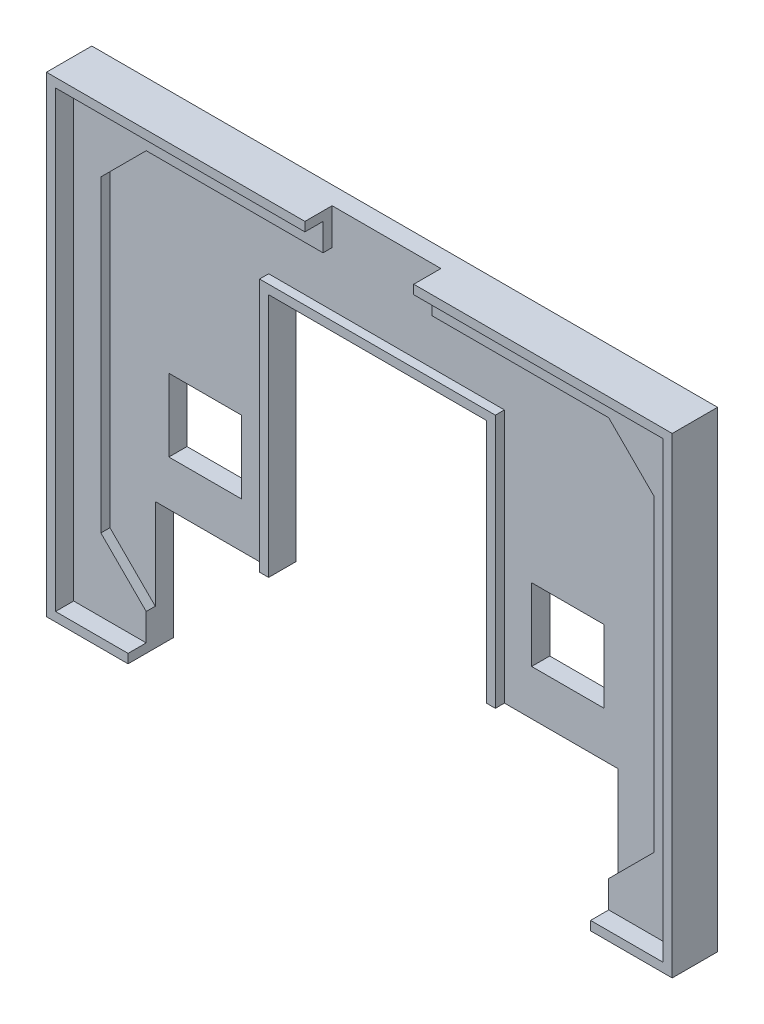
SolidWorks part; units mm, degrees
ref_plane "Přední rovina" through (0, 0, 0) normal (0, 0, 1) x (1, 0, 0)
ref_plane "Horní rovina" through (0, 0, 0) normal (0, 1, 0) x (1, 0, 0)
ref_plane "Pravá rovina" through (0, 0, 0) normal (1, 0, 0) x (0, 0, -1)
sketch "Skica1" plane through (0, 0, 0) normal (0, 0, 1) x (1, 0, 0)
  line L1 (-33.5, -25) -> (33.5, -25)
  line L2 (-33.5, -25) -> (-33.5, 25)
  line L3 (-33.5, 25) -> (33.5, 25)
  line L4 (33.5, -25) -> (33.5, 25)
  line L5 (-33.5, -25) -> (33.5, 25) construction
  line L6 (-33.5, 25) -> (33.5, -25) construction
  point P0 (0, 0)
  dimension "D1" = 67
  dimension "D2" = 50
extrude "Přidat vysunutím1" add sketch "Skica1" along normal blind 3
sketch "Skica2" plane through (0, 0, 3) normal (0, 0, 1) x (1, 0, 0)
  line L0 (-1000, 0) -> (49000, 0) construction
  line L1 (0, -1000) -> (0, 49000) construction
  line L2 (-1000, -22) -> (49000, -22) construction
  line L3 (-25.5, -1000) -> (-25.5, 49000) construction
  line L4 (-30.5, -1000) -> (-30.5, 49000) construction
  line L6 (-33.5, -25) -> (33.5, -25) construction
  line L7 (-25.5, -22) -> (-30.5, -17)
  line L8 (-30.5, -17) -> (-30.5, 17)
  line L9 (-25.5, -22) -> (25.5, -22)
  line L10 (30.5, -17) -> (30.5, 17)
  line L11 (25.5, -22) -> (30.5, -17)
  line L12 (25.5, 22) -> (30.5, 17)
  line L13 (-25.5, 22) -> (25.5, 22)
  line L14 (-25.5, 22) -> (-30.5, 17)
  point P20 (0, -22)
  point P21 (30.5, 0)
  point P24 (-30.5, 0)
  dimension "D1" = 30.5
  dimension "D2" = 5
  dimension "D3" = 3
  dimension "D4" = 45
extrude "Odebrat vysunutím1" cut sketch "Skica2" against normal offset from surface (1 mm away) 2 up to face at (0, 0, 0)
sketch "Skica3" plane through (0, 0, 0) normal (0, 0, -1) x (-1, 0, 0)
  line L0 (0, -1000) -> (0, 49000) construction
  line L1 (33.5, -25) -> (-33.5, -25) construction
  line L2 (24, 1) -> (16, 1)
  line L3 (24, 1) -> (24, -7)
  line L4 (24, -7) -> (16, -7)
  line L5 (16, 1) -> (16, -7)
  line L6 (-16, 1) -> (-16, -7)
  line L7 (33.5, -25) -> (-33.5, -25) construction
  line L8 (25.5, -25) -> (-25.5, -25)
  line L9 (25.5, -25) -> (25.5, -12)
  line L11 (-25.5, -25) -> (-25.5, -12)
  line L12 (-24, -7) -> (-16, -7)
  line L13 (25.5, -12) -> (12, -12)
  line L15 (12, -12) -> (12, 15)
  line L16 (12, 15) -> (-12, 15)
  line L17 (-12, -12) -> (-12, 15)
  line L18 (-12, -12) -> (-25.5, -12)
  line L19 (-24, 1) -> (-24, -7)
  line L20 (-24, 1) -> (-16, 1)
  dimension "D1" = 16
  dimension "D2" = 8
  dimension "D3" = 18
  dimension "D4" = 13
  dimension "D5" = 51
  dimension "D6" = 24
  dimension "D7" = 27
extrude "Odebrat vysunutím2" cut sketch "Skica3" against normal through all
sketch "Skica4" plane through (0, 0, 2) normal (0, 0, 1) x (1, 0, 0)
  line L0 (12, 15) -> (12, -12) construction
  line L1 (-12, -12) -> (-12, 15) construction
  line L2 (-12, 15) -> (12, 15) construction
  line L3 (12, 15) -> (12, -12)
  line L4 (-12, -12) -> (-12, 15)
  line L5 (-12, 15) -> (12, 15)
extrude "Vysunout tenkostěnný1" add sketch "Skica4" along normal up to surface (1 mm away) thin up to face at (0, -3.5714, 3) thin type one direction reverse wall 1
sketch "Skica5" plane through (0, 0, 0) normal (0, 0, -1) x (-1, 0, 0)
  line L0 (-33.5, 25) -> (33.5, 25) construction
  line L1 (33.5, 25) -> (33.5, -25) construction
  line L2 (33.5, -25) -> (25.5, -25) construction
  line L3 (-33.5, -25) -> (-33.5, 25) construction
  line L4 (-25.5, -25) -> (-33.5, -25) construction
  line L5 (-33.5, 25) -> (33.5, 25)
  line L6 (33.5, 25) -> (33.5, -25)
  line L7 (33.5, -25) -> (25.5, -25)
  line L8 (-33.5, -25) -> (-33.5, 25)
  line L9 (-25.5, -25) -> (-33.5, -25)
extrude "Vysunout tenkostěnný2" add sketch "Skica5" against normal blind 5 thin thin type one direction reverse wall 1
sketch "Skica6" plane through (0, 0, 2) normal (0, 0, 1) x (1, 0, 0)
  line L0 (0, -1000) -> (0, 49000) construction
  line L1 (25.5, 22) -> (-25.5, 22) construction
  line L2 (-6, 22) -> (6, 22)
  line L3 (-6, 22) -> (-6, 26)
  line L4 (-6, 26) -> (6, 26)
  line L5 (6, 22) -> (6, 26)
  line L6 (34.5, 26) -> (-34.5, 26) construction
  dimension "D1" = 12
extrude "Odebrat vysunutím3" cut sketch "Skica6" along normal through all
sketch "Skica7" plane through (0, 0, 0) normal (0, 0, -1) x (-1, 0, 0)
  line L0 (-6.0286, 195.0087) -> (293.9714, 195.0087) construction
  line L1 (-28.75, 22) -> (-26.75, 22)
  line L2 (-26.75, 22) -> (-26.75, 21)
  line L3 (-26.75, 21) -> (-25.75, 21)
  line L4 (-25.75, 21) -> (-25.75, 16)
  line L5 (-25.75, 16) -> (-20.75, 16)
  line L6 (-20.75, 16) -> (-20.75, 21)
  line L7 (-20.75, 21) -> (-19.75, 21)
  line L8 (-19.75, 21) -> (-19.75, 22)
  line L9 (-19.75, 22) -> (-17.75, 22)
  line L10 (-17.75, 22) -> (-17.75, 21)
  line L11 (-17.75, 21) -> (-16.75, 21)
  line L12 (-16.75, 21) -> (-16.75, 14)
  line L13 (-16.75, 14) -> (-15.75, 14)
  line L14 (-15.75, 14) -> (-15.75, 8)
  line L21 (-18.75, 5) -> (-27.75, 5)
  line L22 (-27.75, 5) -> (-27.75, 6)
  line L23 (-27.75, 6) -> (-28.75, 6)
  line L24 (-28.75, 6) -> (-28.75, 7)
  line L25 (-28.75, 7) -> (-29.75, 7)
  line L26 (-29.75, 7) -> (-29.75, 8)
  line L27 (-29.75, 8) -> (-30.75, 8)
  line L28 (-30.75, 8) -> (-30.75, 14)
  line L29 (-30.75, 14) -> (-29.75, 14)
  line L30 (-29.75, 14) -> (-29.75, 21)
  line L31 (-29.75, 21) -> (-28.75, 21)
  line L32 (-28.75, 21) -> (-28.75, 22)
  line L33 (-34.5, 26) -> (34.5, 26) construction
  line L34 (-12, 15) -> (-12, -12) construction
  line L35 (-15.75, 8) -> (-16.75, 8)
  line L36 (-16.75, 8) -> (-16.75, 7)
  line L37 (0, 0) -> (0, 29.4657) construction
  line L38 (-16.75, 7) -> (-17.75, 7)
  line L39 (-17.75, 7) -> (-17.75, 6)
  line L40 (-17.75, 6) -> (-18.75, 6)
  line L41 (-18.75, 6) -> (-18.75, 5)
  line L42 (18.75, 6) -> (18.75, 5)
  line L43 (17.75, 6) -> (18.75, 6)
  line L44 (17.75, 7) -> (17.75, 6)
  line L45 (16.75, 7) -> (17.75, 7)
  line L46 (16.75, 8) -> (16.75, 7)
  line L47 (15.75, 8) -> (16.75, 8)
  line L48 (15.75, 14) -> (15.75, 8)
  line L49 (16.75, 14) -> (15.75, 14)
  line L50 (16.75, 21) -> (16.75, 14)
  line L51 (17.75, 21) -> (16.75, 21)
  line L52 (17.75, 22) -> (17.75, 21)
  line L53 (19.75, 22) -> (17.75, 22)
  line L54 (19.75, 21) -> (19.75, 22)
  line L55 (20.75, 21) -> (19.75, 21)
  line L56 (20.75, 16) -> (20.75, 21)
  line L57 (25.75, 16) -> (20.75, 16)
  line L58 (25.75, 21) -> (25.75, 16)
  line L59 (26.75, 21) -> (25.75, 21)
  line L60 (26.75, 22) -> (26.75, 21)
  line L61 (28.75, 22) -> (26.75, 22)
  line L62 (28.75, 21) -> (28.75, 22)
  line L63 (29.75, 21) -> (28.75, 21)
  line L64 (29.75, 14) -> (29.75, 21)
  line L65 (30.75, 14) -> (29.75, 14)
  line L66 (30.75, 8) -> (30.75, 14)
  line L67 (29.75, 8) -> (30.75, 8)
  line L68 (29.75, 7) -> (29.75, 8)
  line L69 (28.75, 7) -> (29.75, 7)
  line L70 (28.75, 6) -> (28.75, 7)
  line L71 (27.75, 6) -> (28.75, 6)
  line L72 (27.75, 5) -> (27.75, 6)
  line L73 (18.75, 5) -> (27.75, 5)
  dimension "D1" = 2
  dimension "D2" = 1
  dimension "D3" = 5
  dimension "D4" = 5
  dimension "D5" = 1
  dimension "D6" = 2
  dimension "D7" = 1
  dimension "D8" = 1
  dimension "D9" = 1
  dimension "D10" = 1
  dimension "D11" = 1
  dimension "D12" = 1
  dimension "D13" = 7
  dimension "D14" = 7
  dimension "D15" = 1
  dimension "D16" = 1
  dimension "D17" = 6
  dimension "D18" = 6
  dimension "D19" = 1
  dimension "D20" = 1
  dimension "D21" = 1
  dimension "D22" = 1
  dimension "D23" = 1
  dimension "D24" = 1
  dimension "D25" = 1
  dimension "D26" = 1
  dimension "D27" = 1
  dimension "D28" = 1
  dimension "D29" = 1
  dimension "D30" = 1
  dimension "D31" = 4
  dimension "D32" = 3.75
extrude "Odebrat vysunutím4" cut sketch "Skica7" against normal blind 1
sketch "Skica8" plane through (0, 0, 0) normal (0, 0, -1) x (-1, 0, 0)
  line L0 (-30.75, 14) -> (-30.75, 8) construction
  line L1 (-27.75, 12) -> (-25.75, 12)
  line L2 (-27.75, 12) -> (-27.75, 10)
  line L3 (-27.75, 10) -> (-25.75, 10)
  line L4 (-25.75, 12) -> (-25.75, 10)
  line L5 (-29.75, 14) -> (-30.75, 14) construction
  line L6 (-23.25, 16) -> (-23.25, 4.1822) construction
  line L7 (-20.75, 16) -> (-25.75, 16) construction
  line L8 (-18.75, 10) -> (-20.75, 10)
  line L9 (-20.75, 12) -> (-20.75, 10)
  line L10 (-18.75, 12) -> (-20.75, 12)
  line L11 (-18.75, 12) -> (-18.75, 10)
  line L13 (-23.75, 10) -> (-22.75, 10)
  line L14 (-22.75, 10) -> (-22.75, 9)
  line L15 (-22.75, 9) -> (-21.75, 9)
  line L16 (-21.75, 9) -> (-21.75, 8)
  line L17 (-21.75, 8) -> (-24.75, 8)
  line L18 (-24.75, 8) -> (-24.75, 9)
  line L19 (-24.75, 9) -> (-23.75, 9)
  line L20 (-23.75, 9) -> (-23.75, 10)
  line L22 (0, 0) -> (0, 28.6399) construction
  line L23 (24.75, 9) -> (23.75, 9)
  line L24 (24.75, 8) -> (24.75, 9)
  line L25 (21.75, 8) -> (24.75, 8)
  line L26 (21.75, 9) -> (21.75, 8)
  line L27 (22.75, 9) -> (21.75, 9)
  line L28 (22.75, 10) -> (22.75, 9)
  line L29 (23.75, 10) -> (22.75, 10)
  line L30 (23.75, 9) -> (23.75, 10)
  line L31 (27.75, 10) -> (25.75, 10)
  line L32 (25.75, 12) -> (25.75, 10)
  line L33 (27.75, 12) -> (25.75, 12)
  line L34 (27.75, 12) -> (27.75, 10)
  line L35 (18.75, 12) -> (18.75, 10)
  line L36 (18.75, 12) -> (20.75, 12)
  line L37 (20.75, 12) -> (20.75, 10)
  line L38 (18.75, 10) -> (20.75, 10)
  dimension "D1" = 2
  dimension "D2" = 2
  dimension "D3" = 3
  dimension "D4" = 4
  dimension "D5" = 1
  dimension "D6" = 1
  dimension "D7" = 1
  dimension "D8" = 1
  dimension "D9" = 1
  dimension "D10" = 0
  dimension "D11" = 1
  dimension "D12" = 1
extrude "Přidat vysunutím2" add sketch "Skica8" along normal blind 1 from offset 1 offset against normal yes
sketch "Skica9" plane through (0, 0, 0) normal (0, 0, -1) x (-1, 0, 0)
  line L0 (-11.2, 23.3) -> (-9.6, 23.3)
  line L1 (-9.6, 23.3) -> (-9.6, 19.3)
  line L2 (-9.6, 19.3) -> (-8.8, 19.3)
  line L3 (-8.8, 19.3) -> (-8.8, 21.7)
  line L4 (-8.8, 21.7) -> (-8, 21.7)
  line L5 (-8, 21.7) -> (-8, 19.3)
  line L6 (-8, 19.3) -> (-7.2, 19.3)
  line L7 (-7.2, 19.3) -> (-7.2, 23.3)
  line L8 (-7.2, 23.3) -> (-5.6, 23.3)
  line L9 (-5.6, 23.3) -> (-5.6, 18.5)
  line L10 (-5.6, 18.5) -> (-6.4, 18.5)
  line L11 (-6.4, 18.5) -> (-6.4, 17.7)
  line L12 (-6.4, 17.7) -> (-8, 17.7)
  line L13 (-8, 17.7) -> (-8, 18.5)
  line L14 (-8, 18.5) -> (-8.8, 18.5)
  line L15 (-8.8, 18.5) -> (-8.8, 17.7)
  line L16 (-8.8, 17.7) -> (-10.4, 17.7)
  line L17 (-10.4, 17.7) -> (-10.4, 18.5)
  line L18 (-10.4, 18.5) -> (-11.2, 18.5)
  line L19 (-11.2, 18.5) -> (-11.2, 23.3)
  line L20 (-4.8, 23.3) -> (-3.2, 23.3)
  line L21 (-3.2, 23.3) -> (-3.2, 20.9)
  line L22 (-3.2, 20.9) -> (-1.6, 20.9)
  line L23 (-1.6, 20.9) -> (-1.6, 23.3)
  line L24 (-1.6, 23.3) -> (0, 23.3)
  line L25 (0, 23.3) -> (0, 17.7)
  line L26 (0, 17.7) -> (-1.6, 17.7)
  line L27 (-1.6, 17.7) -> (-1.6, 20.1)
  line L28 (-1.6, 20.1) -> (-3.2, 20.1)
  line L29 (-3.2, 20.1) -> (-3.2, 17.7)
  line L30 (-3.2, 17.7) -> (-4.8, 17.7)
  line L31 (-4.8, 17.7) -> (-4.8, 23.3)
  line L32 (1.6, 23.3) -> (4.8, 23.3)
  line L33 (4.8, 23.3) -> (4.8, 22.5)
  line L34 (4.8, 22.5) -> (5.6, 22.5)
  line L35 (5.6, 22.5) -> (5.6, 18.5)
  line L36 (5.6, 18.5) -> (4.8, 18.5)
  line L37 (4.8, 18.5) -> (4.8, 17.7)
  line L38 (4.8, 17.7) -> (1.6, 17.7)
  line L39 (1.6, 17.7) -> (1.6, 18.5)
  line L40 (1.6, 18.5) -> (0.8, 18.5)
  line L41 (0.8, 18.5) -> (0.8, 22.5)
  line L42 (0.8, 22.5) -> (1.6, 22.5)
  line L45 (6.4, 23.3) -> (10.4, 23.3)
  line L46 (10.4, 23.3) -> (10.4, 22.5)
  line L47 (10.4, 22.5) -> (11.2, 22.5)
  line L48 (11.2, 22.5) -> (11.2, 20.9)
  line L49 (11.2, 20.9) -> (10.4, 20.9)
  line L50 (10.4, 20.9) -> (10.4, 20.1)
  line L51 (10.4, 20.1) -> (8, 20.1)
  line L52 (8, 20.1) -> (8, 17.7)
  line L53 (8, 17.7) -> (6.4, 17.7)
  line L54 (6.4, 17.7) -> (6.4, 23.3)
  line L55 (-34.5, 26) -> (34.5, 26) construction
  line L56 (-12, 15) -> (-12, -12) construction
  line L57 (12, 15) -> (-12, 15) construction
  line L58 (1.6, 23.3) -> (1.6, 22.5)
  dimension "D1" = 1.6
  dimension "D2" = 1.6
  dimension "D3" = 0.8
  dimension "D4" = 0.8
  dimension "D5" = 4.8
  dimension "D6" = 1.6
  dimension "D7" = 1.6
  dimension "D8" = 0.8
  dimension "D9" = 2.7
  dimension "D10" = 0.8
  dimension "D11" = 4
  dimension "D12" = 0.8
  dimension "D13" = 2.7
  dimension "D14" = 2.7
  dimension "D15" = 0.8
  dimension "D16" = 4
  dimension "D17" = 0.8
  dimension "D18" = 0.8
  dimension "D19" = 0.8
  dimension "D20" = 2.4
  dimension "D21" = 0.8
  dimension "D22" = 1.6
  dimension "D23" = 1.6
  dimension "D24" = 2.4
  dimension "D25" = 2.4
  dimension "D26" = 1.6
  dimension "D27" = 1.6
  dimension "D28" = 2.4
  dimension "D29" = 2.4
  dimension "D30" = 2.7
  dimension "D31" = 0.8
  dimension "D32" = 0.8
  dimension "D33" = 0.8
  dimension "D34" = 0.8
  dimension "D35" = 0.8
  dimension "D36" = 0.8
  dimension "D37" = 0.8
  dimension "D38" = 0.8
  dimension "D39" = 0.8
  dimension "D40" = 3.2
  dimension "D41" = 1.6
  dimension "D42" = 5.6
  dimension "D43" = 0.8
  dimension "D44" = 0.8
  dimension "D45" = 0.8
  dimension "D46" = 0.8
  dimension "D47" = 0.8
  dimension "D48" = 2.4
  dimension "D49" = 1.6
extrude "Odebrat vysunutím5" cut sketch "Skica9" against normal blind 1
sketch "Skica10" plane through (0, 0, 0) normal (0, 0, -1) x (-1, 0, 0)
  line L0 (4.8, 23.3) -> (1.6, 23.3) construction
  line L1 (2.4, 21.7) -> (4, 21.7)
  line L2 (2.4, 21.7) -> (2.4, 19.3)
  line L3 (2.4, 19.3) -> (4, 19.3)
  line L4 (4, 21.7) -> (4, 19.3)
  line L5 (8, 22.5) -> (9.6, 22.5)
  line L6 (8, 22.5) -> (8, 20.9)
  line L7 (8, 20.9) -> (9.6, 20.9)
  line L8 (9.6, 22.5) -> (9.6, 20.9)
  line L9 (1.6, 17.7) -> (4.8, 17.7) construction
  line L10 (0.8, 22.5) -> (0.8, 18.5) construction
  line L11 (5.6, 18.5) -> (5.6, 22.5) construction
  line L12 (8, 20.1) -> (10.4, 20.1) construction
  line L13 (10.4, 23.3) -> (6.4, 23.3) construction
  line L14 (6.4, 23.3) -> (6.4, 17.7) construction
  line L15 (11.2, 20.9) -> (11.2, 22.5) construction
  dimension "D1" = 1.6
  dimension "D2" = 1.6
  dimension "D3" = 1.6
  dimension "D4" = 1.6
  dimension "D5" = 0.8
  dimension "D6" = 0.8
  dimension "D7" = 1.6
  dimension "D8" = 1.6
extrude "Přidat vysunutím3" add sketch "Skica10" along normal blind 1 from offset 1 offset against normal yes
